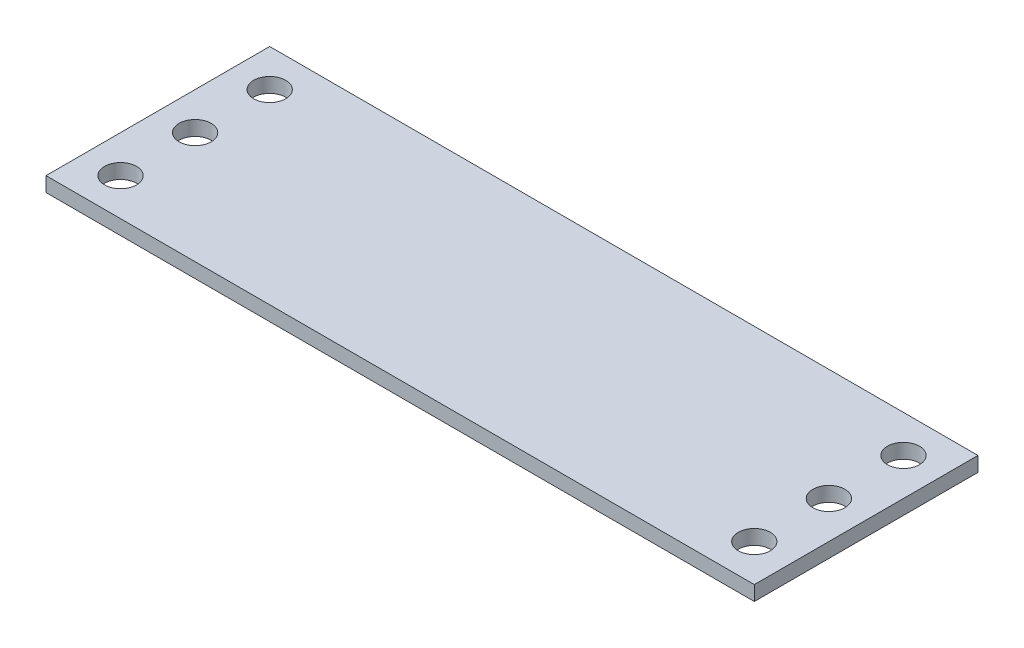
SolidWorks part; units mm, degrees
ref_plane "Front Plane" through (0, 0, 0) normal (0, 0, 1) x (1, 0, 0)
ref_plane "Top Plane" through (0, 0, 0) normal (0, 1, 0) x (1, 0, 0)
ref_plane "Right Plane" through (0, 0, 0) normal (1, 0, 0) x (0, 0, -1)
sketch "Sketch1" plane through (0, 0, 0) normal (0, 1, 0) x (1, 0, 0)
  line L1 (-24.13, 7.62) -> (24.13, 7.62)
  line L2 (-24.13, 7.62) -> (-24.13, -7.62)
  line L3 (-24.13, -7.62) -> (24.13, -7.62)
  line L4 (24.13, 7.62) -> (24.13, -7.62)
  line L5 (-24.13, 7.62) -> (24.13, -7.62) construction
  line L6 (-24.13, -7.62) -> (24.13, 7.62) construction
  point P0 (0, 0)
  dimension "D1" = 48.26
  dimension "D2" = 15.24
extrude "Boss-Extrude1" add sketch "Sketch1" along normal blind 1
sketch "Sketch2" plane through (0, 1, 0) normal (0, 1, 0) x (1, 0, 0)
  line L0 (-24.13, 7.62) -> (-24.13, -7.62) construction
  line L1 (24.13, 7.62) -> (-24.13, 7.62) construction
  line L2 (0, 0) -> (0, -7.62) construction
  line L3 (-24.13, -7.62) -> (24.13, -7.62) construction
  circle A0 centre (-21.59, 5.08) radius 1.0922
  circle A1 centre (-21.59, 0) radius 1.0922
  circle A2 centre (-21.59, -5.08) radius 1.0922
  circle A3 centre (21.59, -5.08) radius 1.0922
  circle A4 centre (21.59, 0) radius 1.0922
  circle A5 centre (21.59, 5.08) radius 1.0922
  dimension "D1" = 2.1844
  dimension "D2" = 2.54
  dimension "D3" = 2.54
  dimension "D4" = 3
extrude "Cut-Extrude1" cut sketch "Sketch2" against normal blind 1
